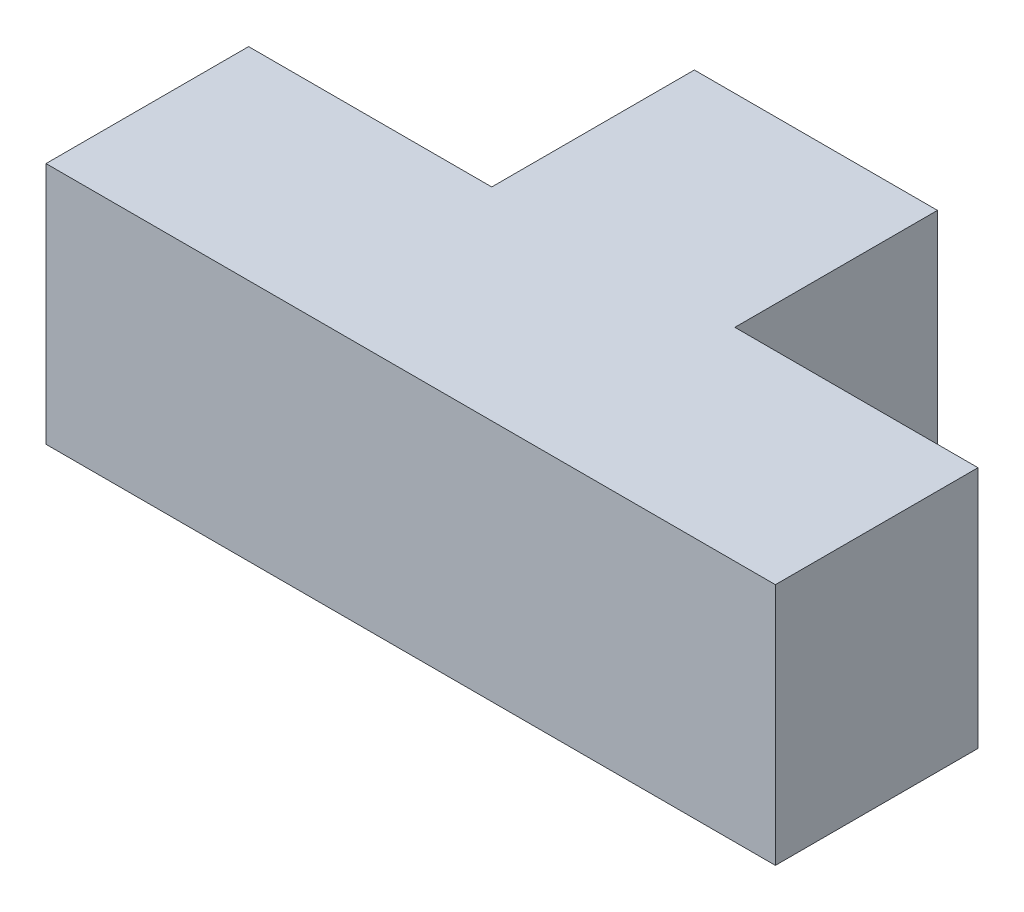
SolidWorks part; units mm, degrees
ref_plane "Front Plane" through (0, 0, 0) normal (0, 0, 1) x (1, 0, 0)
ref_plane "Top Plane" through (0, 0, 0) normal (0, 1, 0) x (1, 0, 0)
ref_plane "Right Plane" through (0, 0, 0) normal (1, 0, 0) x (0, 0, -1)
sketch "Sketch1" plane through (0, 0, 0) normal (0, 1, 0) x (1, 0, 0)
  line L0 (0, 0) -> (0, 25)
  line L1 (0, 25) -> (30, 25)
  line L2 (30, 25) -> (30, 50)
  line L3 (30, 50) -> (60, 50)
  line L4 (60, 50) -> (60, 25)
  line L5 (60, 25) -> (90, 25)
  line L6 (90, 25) -> (90, 0)
  line L7 (90, 0) -> (0, 0)
  dimension "D1" = 90
  dimension "D2" = 25
  dimension "D3" = 30
  dimension "D4" = 25
extrude "Boss-Extrude1" add sketch "Sketch1" along normal blind 30
